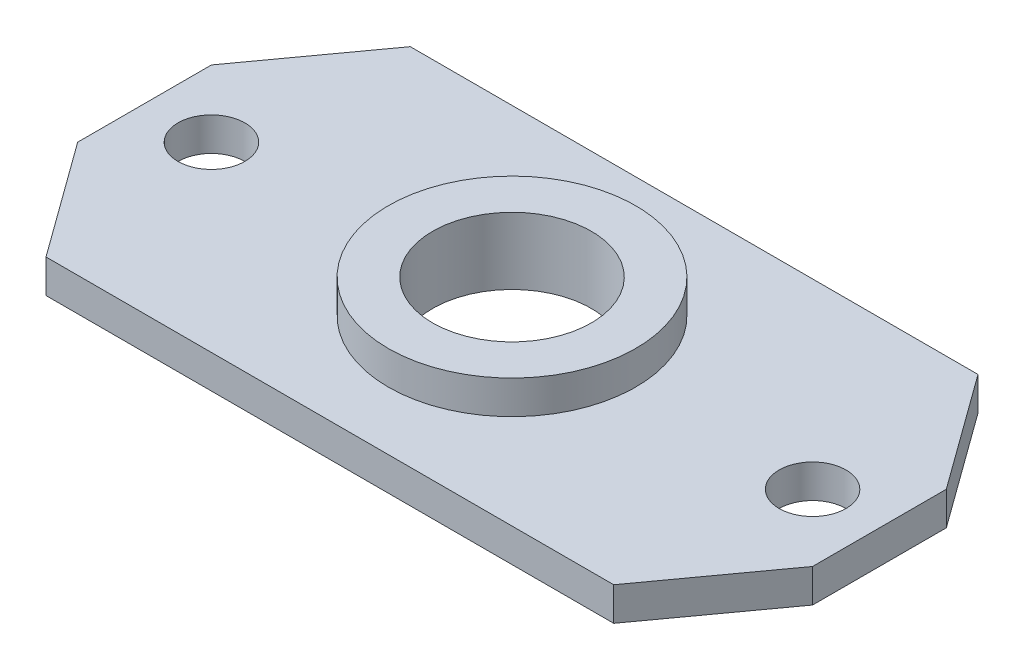
SolidWorks part; units mm, degrees
ref_plane "Front Plane" through (0, 0, 0) normal (0, 0, 1) x (1, 0, 0)
ref_plane "Top Plane" through (0, 0, 0) normal (0, 1, 0) x (1, 0, 0)
ref_plane "Right Plane" through (0, 0, 0) normal (1, 0, 0) x (0, 0, -1)
sketch "Sketch1" plane through (0, 0, 0) normal (0, 1, 0) x (1, 0, 0)
  line L0 (16.98, 21.79) -> (16.98, 0) construction
  line L1 (0, 0) -> (33.96, 0)
  line L3 (0, 21.79) -> (33.96, 21.79)
  line L5 (-5, 10.895) -> (38.96, 10.895) construction
  line L6 (0, 21.79) -> (-5, 14.895)
  line L7 (-5, 14.895) -> (-5, 6.895)
  line L8 (-5, 6.895) -> (0, 0)
  line L9 (33.96, 21.79) -> (38.96, 14.895)
  line L10 (38.96, 14.895) -> (38.96, 6.895)
  line L11 (38.96, 6.895) -> (33.96, 0)
  circle A0 centre (-1, 10.895) radius 2
  circle A1 centre (34.96, 10.895) radius 2
  circle A2 centre (-1, 10.895) radius 2
  circle A3 centre (34.96, 10.895) radius 2
  point P19 (16.98, 10.895)
  point P20 (-7.3818, 6.895)
  point P21 (0, 0)
  point P22 (-2.5, 7.7309)
  point P23 (-1, 10.895)
  dimension "D5" = 4
  dimension "D1" = 33.96
  dimension "D2" = 21.79
  dimension "D3" = 8
  dimension "D4" = 5
  dimension "D6" = 21.79
  dimension "D7" = 4
extrude "Boss-Extrude1" add sketch "Sketch1" along normal blind 2
sketch "Sketch2" plane through (0, 2, 0) normal (0, 1, 0) x (1, 0, 0)
  line L0 (-5, 10.895) -> (38.96, 10.895) construction
  line L3 (38.96, 14.895) -> (38.96, 6.895) construction
  line L6 (-5, 14.895) -> (-5, 6.895) construction
  circle A0 centre (16.98, 10.895) radius 7.4
  point P2 (38.96, 10.895)
  point P5 (-5, 10.895)
  point P6 (16.98, 10.895)
  point P7 (0, 10.895)
  dimension "D1" = 14.8
extrude "Boss-Extrude2" add sketch "Sketch2" along normal blind 2
sketch "Sketch3" plane through (0, 4, 0) normal (0, 1, 0) x (1, 0, 0)
  circle A0 centre (16.98, 10.895) radius 4.75
  dimension "D1" = 9.5
extrude "Cut-Extrude1" cut sketch "Sketch3" against normal through all
equation "\"8mm hole\" = 8.6mm"
equation "\"22mm hole\"= 23mm"
equation "\"15mm hole\"= 15.8mm"
equation "\"bed height offset\"= 3mm"
equation "\"D1@Sketch2\"=\"15mm hole\" - 1"
